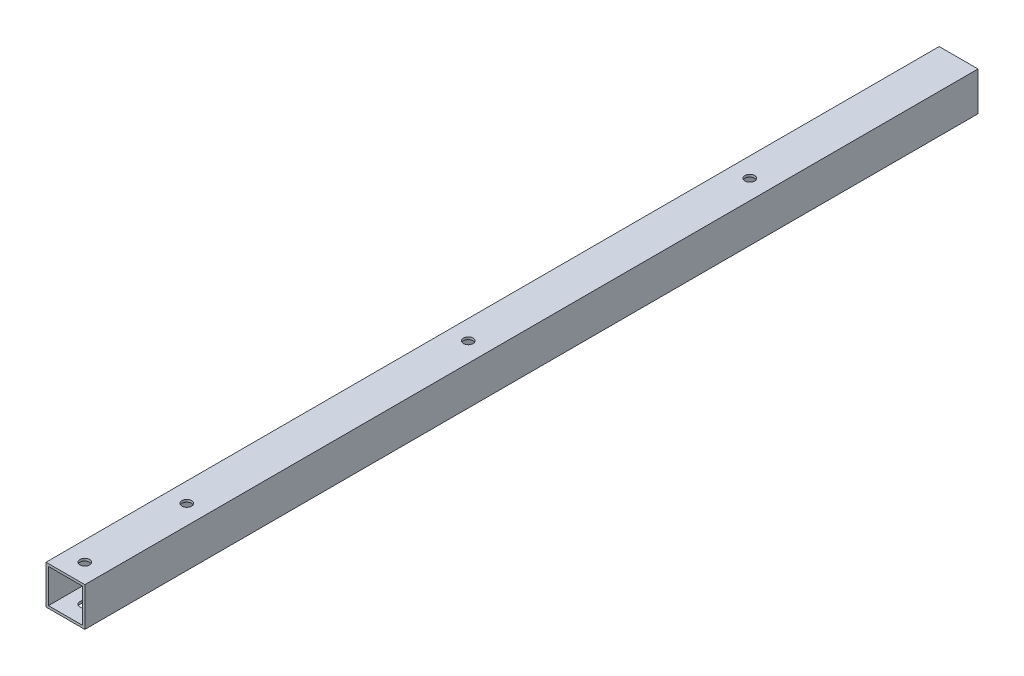
SolidWorks part; units mm, degrees
ref_plane "Front Plane" through (0, 0, 0) normal (0, 0, 1) x (1, 0, 0)
ref_plane "Top Plane" through (0, 0, 0) normal (0, 1, 0) x (1, 0, 0)
ref_plane "Right Plane" through (0, 0, 0) normal (1, 0, 0) x (0, 0, -1)
sketch "Sketch1" plane through (0, 0, 0) normal (0, 0, 1) x (1, 0, 0)
  line L0 (-536.575, 327.025) -> (-492.125, 327.025)
  line L1 (-539.75, 330.2) -> (-488.95, 330.2)
  line L2 (-539.75, 330.2) -> (-539.75, 279.4)
  line L3 (-539.75, 279.4) -> (-488.95, 279.4)
  line L4 (-488.95, 330.2) -> (-488.95, 279.4)
  line L5 (-492.125, 327.025) -> (-492.125, 282.575)
  line L6 (-536.575, 282.575) -> (-492.125, 282.575)
  line L7 (-536.575, 327.025) -> (-536.575, 282.575)
  line L8 (-584.2, 279.4) -> (-468.774, 279.4) construction
  line L10 (-584.2, -304.8) -> (-584.2, 304.8) construction
  circle A0 centre (-584.2, 304.8) radius 25.4 construction
  circle A1 centre (-584.2, 304.8) radius 25.4 construction
  dimension "D1" = 3.175
  dimension "D2" = 50.8
  dimension "D3" = 44.45
extrude "Extrude1" add sketch "Sketch1" along normal blind 1117.6 and the other way blind 50.8
sketch "Sketch2" plane through (-539.75, 0, 0) normal (-1, 0, 0) x (0, 0, 1)
  line L0 (1117.6, 330.2) -> (1066.8, 279.4)
  line L1 (-50.8, 279.4) -> (1117.6, 279.4) construction
  line L2 (1066.8, 279.4) -> (1117.6, 279.4)
  line L3 (1117.6, 279.4) -> (1117.6, 330.2)
extrude "Cut-Extrude1" [suppressed] cut sketch "Sketch2" against normal through all
sketch "Sketch3" plane through (0, 330.2, 0) normal (0, 1, 0) x (1, 0, 0)
  line L0 (-488.95, -1117.6) -> (-539.75, -1117.6) construction
  line L1 (-514.35, -1117.6) -> (-514.35, -1092.2) construction
  circle A0 centre (-514.35, -1092.2) radius 6.35
  circle A1 centre (-514.35, -958.85) radius 6.35
  circle A2 centre (-514.35, -590.55) radius 6.35
  circle A3 centre (-514.35, -222.25) radius 6.35
  dimension "D2" = 12.7
  dimension "D3" = 12.7
  dimension "D1" = 25.4
extrude "Cut-Extrude2" cut sketch "Sketch3" against normal through all
